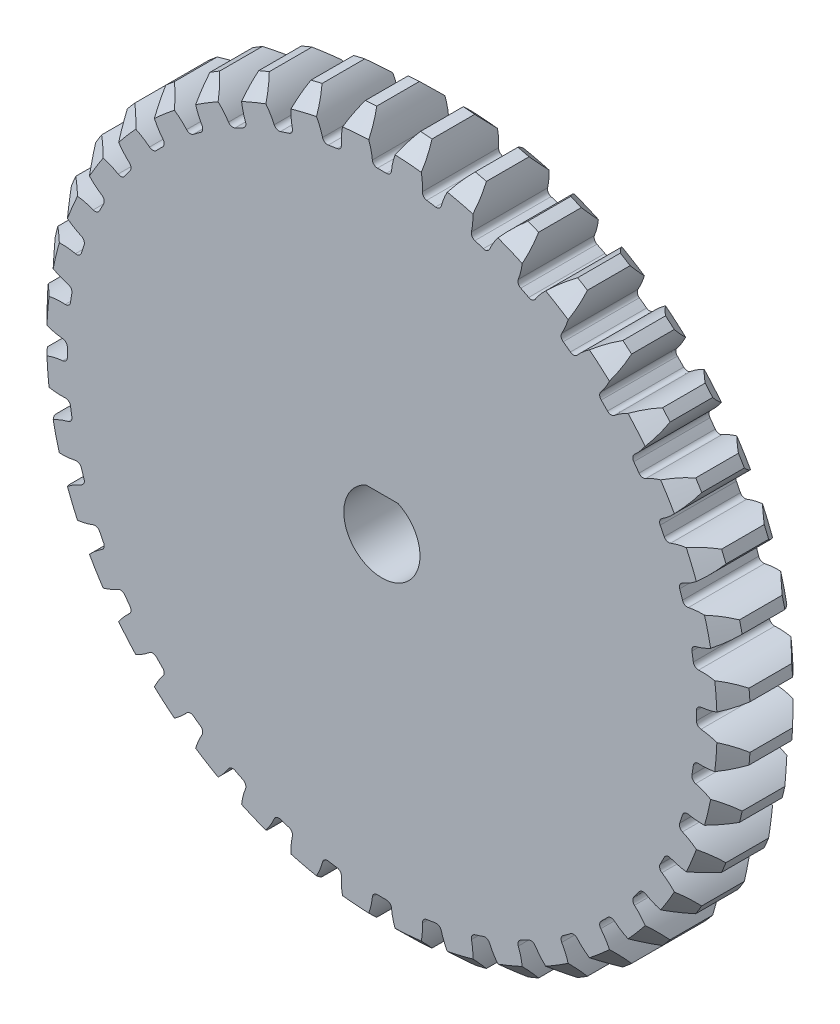
SolidWorks part; units mm, degrees
ref_plane "Front Plane" through (0, 0, 0) normal (0, 0, 1) x (1, 0, 0)
ref_plane "Top Plane" through (0, 0, 0) normal (0, 1, 0) x (1, 0, 0)
ref_plane "Right Plane" through (0, 0, 0) normal (1, 0, 0) x (0, 0, -1)
sketch "Sketch1" plane through (0, 0, 0) normal (0, 0, 1) x (1, 0, 0)
  circle A0 centre (0, 0) radius 44 construction
  circle A1 centre (0, 0) radius 46.2
  dimension "D1" = 88
  dimension "D2" = 92.4
extrude "Boss-Extrude1" add sketch "Sketch1" along normal mid plane 10
sketch "Sketch2" plane through (0, 0, 0) normal (0, 0, 1) x (1, 0, 0)
  line L0 (0, 0) -> (0, 46.2) construction
  line L1 (0, 0) -> (7.2273, 45.6312) construction
  line L2 (0, 0) -> (3.6248, 46.0576) construction
  line L3 (-1.2134, 41.2822) -> (0, 0) construction
  line L4 (-1.7274, 43.9661) -> (1.7274, 43.9661) construction
  line L5 (1.7274, 43.9661) -> (5.1716, 43.695) construction
  line L6 (-2.5156, 46.1315) -> (0, 39.22) construction
  circle A0 centre (0, 0) radius 41.8 construction
  circle A2 centre (0, 0) radius 46.2 construction
  arc A3 (-2.8745, 46.1105) -> (-1.2134, 41.2822) centre (-9.7944, 41.0299) cw
  circle A4 centre (0, 0) radius 46.2 construction
  arc A5 (2.8745, 46.1105) -> (1.2134, 41.2822) centre (9.7944, 41.0299) ccw
  circle A6 centre (0, 0) radius 44 construction
  arc A7 (1.2134, 41.2822) -> (-1.2134, 41.2822) centre (0, 0) ccw
  arc A8 (2.8745, 46.1105) -> (-2.8745, 46.1105) centre (0, 0) ccw
  dimension "D1" = 9
  dimension "D2" = 4.4
  dimension "D4" = 20
  dimension "D3" = 0.5
extrude "Cut-Extrude1" cut sketch "Sketch2" against normal through all both and the other way through all contours A5 A8 A3 A7
fillet "Fillet1" radius 0.66 2 edges at (1.2134, 41.2822, 0) (-1.2134, 41.2822, 0)
chamfer "Chamfer1" distance 2.2 angle 45 2 edges at (0, -46.2, -5) (0, -46.2, 5)
pattern_circular "CirPattern1" count 40 over 360 about axis through (0, 0, 0) along (0, 0, 1) of "Fillet1", "Cut-Extrude1"
sketch "Sketch3" plane through (0, 0, 5) normal (0, 0, 1) x (1, 0, 0)
  line L2 (-2, 4.5826) -> (-2, 7)
  line L3 (-2, 7) -> (2, 7)
  line L4 (2, 4.5826) -> (2, 7)
  arc A0 (-2, 4.5826) -> (2, 4.5826) centre (0, 0) ccw
  point P3 (0, 5)
  point P5 (0, 7)
  dimension "D1" = 10
  dimension "D2" = 2
  dimension "D3" = 4
extrude "Cut-Extrude2" cut sketch "Sketch3" against normal through all
fillet "Fillet2" radius 0.2 12 edges at (0, -5, 5) (0, -5, -5) (-2, 4.5826, 0) (2, 4.5826, 0) (0, 7, -5) (0, 7, 5) (-2, 7, 0) (-2, 5.7913, -5) (-2, 5.7913, 5) (2, 5.7913, -5) (2, 7, 0) (2, 5.7913, 5)
sketch "Sketch4" plane through (0, 0, 0) normal (0, 0, 1) x (1, 0, 0)
  circle A0 centre (0, 0) radius 44
sketch "Sketch5" plane through (0, 0, -5) normal (0, 0, -1) x (-1, 0, 0)
  line L0 (-2.1154, 4.5305) -> (2.1154, 4.5305)
  arc A0 (-2.1154, 4.5305) -> (2.1154, 4.5305) centre (0, 0) ccw
  circle A1 centre (0, 0) radius 10
  dimension "D2" = 5
extrude "Boss-Extrude2" add sketch "Sketch5" along normal blind 9 and the other way up to surface
sketch "Sketch6" plane through (0, 0, 0) normal (0, 1, 0) x (1, 0, 0)
  line L0 (5, 14) -> (-5, 14) construction
  circle A0 centre (0, 10) radius 1.15
  point P4 (0, 0)
  dimension "D1" = 2.3
  dimension "D2" = 4
extrude "Cut-Extrude3" cut sketch "Sketch6" along normal through all
equation "\"Module\"= 2.2"
equation "\"Number of Teeth\"= 40'Number of Teeth"
equation "\"Pressure Angle\"= 20"
equation "\"D1@Sketch1\"=\"Module\" * \"Number of Teeth\""
equation "\"D2@Sketch1\"=( \"Number of Teeth\" + 2) * \"Module\""
equation "\"D1@Sketch2\"=360 / \"Number of Teeth\""
equation "\"D2@Sketch2\"= \"Module\" * 2"
equation "\"D4@Sketch2\"=\"Pressure Angle\""
equation "\"D1@Fillet1\"=0.3 * \"Module\""
equation "\"D1@CirPattern1\"= \"Number of Teeth\""
equation "\"D1@Chamfer1\"= \"Module\""
equation "\"Gear Thickness\"= 10"
equation "\"D1@Boss-Extrude1\"= \"Gear Thickness\""
